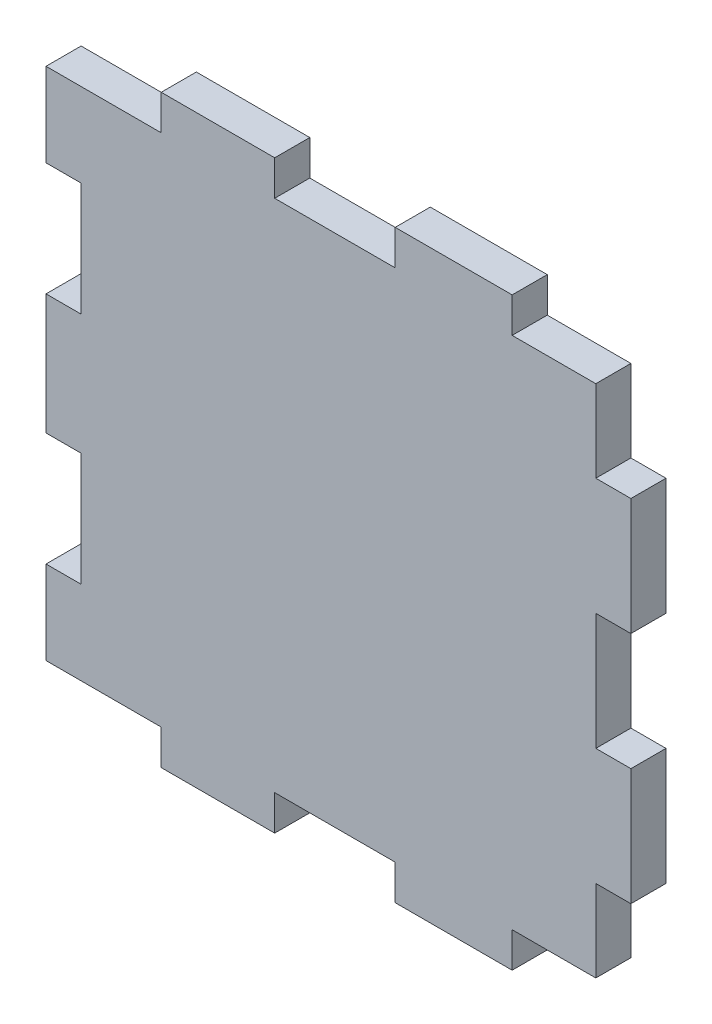
SolidWorks part; units mm, degrees
ref_plane "Alzado" through (0, 0, 0) normal (0, 0, 1) x (1, 0, 0)
ref_plane "Planta" through (0, 0, 0) normal (0, 1, 0) x (1, 0, 0)
ref_plane "Vista lateral" through (0, 0, 0) normal (1, 0, 0) x (0, 0, -1)
sketch "Croquis1" plane through (0, 0, 0) normal (0, 0, 1) x (1, 0, 0)
  line L0 (-16.65, 22) -> (-26.5, 22)
  line L1 (-26.5, -25) -> (-16.65, -25) construction
  line L2 (-26.5, -25) -> (-26.5, -14.85) construction
  line L3 (-26.5, 25) -> (-16.65, 25) construction
  line L4 (26.5, -25) -> (26.5, -5) construction
  line L5 (-26.5, 22) -> (-26.5, 25) construction
  line L6 (-23.32, 22) -> (20.5, -19.3396) construction
  line L7 (-23.5, 0) -> (23.5, 0) construction
  line L8 (26.5, 15) -> (23.5, 15) construction
  line L10 (26.5, 5) -> (23.5, 5) construction
  line L11 (23.5, 15) -> (23.5, 5)
  line L17 (23.5, -15) -> (23.5, -5)
  line L18 (26.5, -5) -> (23.5, -5) construction
  line L19 (26.5, -5) -> (26.5, 5) construction
  line L20 (26.5, 15) -> (26.5, 25) construction
  line L21 (23.5, 5) -> (23.5, 10) construction
  line L22 (-26.5, 14.85) -> (-23.5, 14.85)
  line L24 (-26.5, 5.15) -> (-23.5, 5.15)
  line L25 (-23.5, 14.85) -> (-23.5, 5.15)
  line L26 (-23.5, 5.15) -> (-23.5, 10) construction
  line L27 (23.5, 10) -> (-23.5, 10) construction
  line L28 (-26.5, 14.85) -> (-26.5, 22)
  line L29 (-26.5, -5.15) -> (-23.5, -5.15)
  line L30 (-23.5, -14.85) -> (-23.5, -5.15)
  line L31 (-26.5, -14.85) -> (-23.5, -14.85)
  line L32 (-26.5, -5.15) -> (-26.5, 5.15)
  line L33 (-6.95, -25) -> (3.35, -25) construction
  line L35 (-16.65, -25) -> (-16.65, -22) construction
  line L36 (-16.65, -22) -> (-6.95, -22) construction
  line L37 (-6.95, -25) -> (-6.95, -22)
  line L38 (3.35, -25) -> (3.35, -22) construction
  line L39 (13.35, -22) -> (3.35, -22) construction
  line L40 (13.35, -25) -> (13.35, -22) construction
  line L41 (13.35, -25) -> (20.5, -25) construction
  line L42 (13.35, 25) -> (13.35, 22)
  line L43 (13.35, 22) -> (3.35, 22) construction
  line L44 (3.35, 25) -> (3.35, 22)
  line L45 (-6.95, 25) -> (-6.95, 22)
  line L46 (-16.65, 22) -> (-6.95, 22) construction
  line L47 (-16.65, 25) -> (-16.65, 22)
  line L49 (13.35, 25) -> (20.5, 25) construction
  line L50 (13.35, 25) -> (20.5, 25) construction
  line L51 (23.5, 5) -> (20.5, 5)
  line L52 (23.5, 5) -> (23.5, -5) construction
  line L53 (23.5, -5) -> (20.5, -5)
  line L54 (20.5, 5) -> (20.5, -5)
  line L55 (23.5, -15) -> (20.5, -15)
  line L58 (20.5, -15) -> (20.5, -25) construction
  line L59 (23.5, 15) -> (20.5, 15)
  line L62 (20.5, 15) -> (20.5, 22)
  line L63 (20.5, -25) -> (13.35, -25) construction
  line L64 (20.5, -25) -> (25, -25) construction
  line L65 (25, -25) -> (26.5, -25) construction
  line L66 (20.5, -19.3396) -> (26.5, -25) construction
  line L67 (23.5, 0) -> (28, 0) construction
  line L68 (-26.5, 25) -> (-23.32, 22) construction
  line L69 (-16.65, 25) -> (-6.95, 25)
  line L70 (3.35, 25) -> (13.35, 25)
  line L71 (13.35, 22) -> (20.5, 22)
  line L72 (20.5, 22) -> (20.5, 25) construction
  line L73 (-6.95, 22) -> (3.35, 22)
  line L74 (13.35, -22) -> (20.5, -22)
  line L75 (13.35, -25) -> (13.35, -22)
  line L76 (3.35, -25) -> (13.35, -25)
  line L77 (3.35, -25) -> (3.35, -22)
  line L78 (-6.95, -22) -> (3.35, -22)
  line L79 (-16.65, -25) -> (-6.95, -25)
  line L80 (-16.65, -25) -> (-16.65, -22)
  line L81 (-16.65, -22) -> (-26.5, -22)
  line L82 (20.5, -15) -> (20.5, -22)
  line L83 (-26.5, -14.85) -> (-26.5, -22)
  point P0 (0, 0)
  point P44 (23.5, -10)
  point P54 (0, 0)
  point P57 (0, 0)
  point P62 (0, 0)
  point P67 (13.35, -23.5)
  dimension "D5" = 9.7
  dimension "D6" = 3
  dimension "D7" = 3
  dimension "D8" = 9.7
  dimension "D3" = 3
  dimension "D10" = 50
  dimension "D2" = 50
  dimension "D11" = 3
  dimension "D12" = 10
  dimension "D4" = 10
  dimension "D9" = 3
  dimension "D13" = 10.15
  dimension "D14" = 10
extrude "Saliente-Extruir1" add sketch "Croquis1" along normal blind 3
equation "\"A\"= 3"
equation "\"B\"= 50"
equation "\"C\"= 10"
equation "\"D\"= 10"
equation "\"D5@Croquis1\"=\"C\"-.3"
equation "\"D6@Croquis1\"=\"A\""
equation "\"D7@Croquis1\"=\"A\""
equation "\"D8@Croquis1\"=\"C\"-.3"
equation "\"D3@Croquis1\"=\"A\""
equation "\"D2@Croquis1\"=\"B\""
equation "\"D11@Croquis1\"=\"A\""
equation "\"D12@Croquis1\"=\"C\""
equation "\"D4@Croquis1\"=\"C\""
equation "\"D9@Croquis1\"=\"A\""
equation "\"D13@Croquis1\"=\"C\"+.15"
